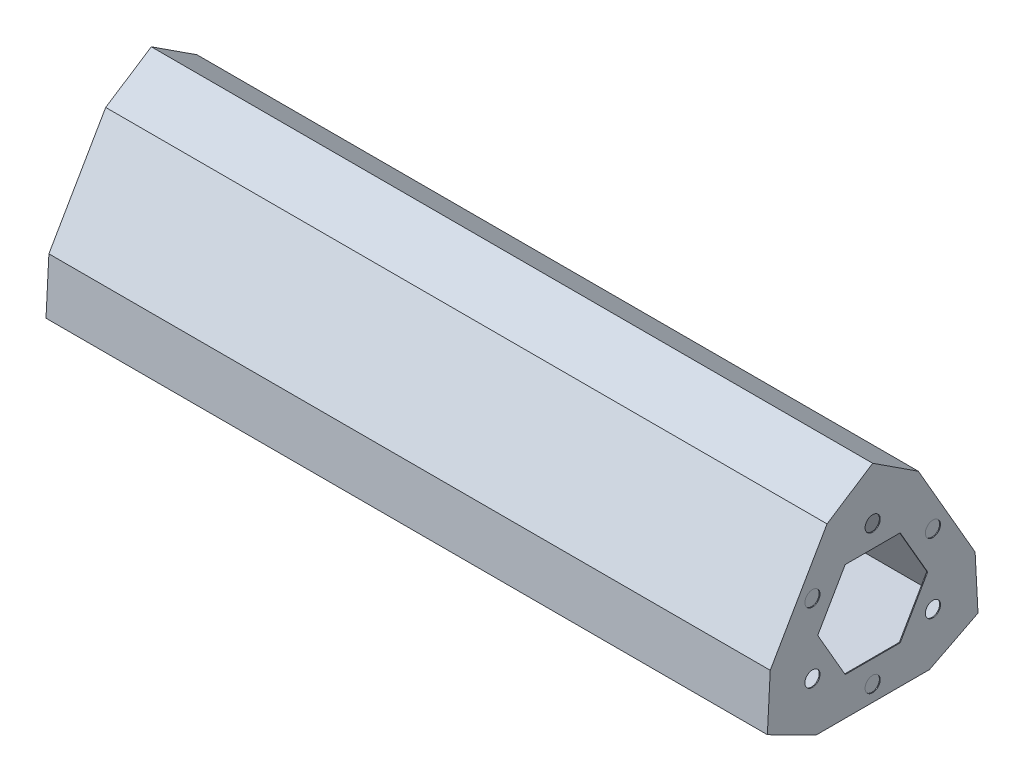
SolidWorks part; units mm, degrees
material "Polyethylene Cross-Linked"
ref_plane "Front Plane" through (0, 0, 0) normal (0, 0, 1) x (1, 0, 0)
ref_plane "Top Plane" through (0, 0, 0) normal (0, 1, 0) x (1, 0, 0)
ref_plane "Right Plane" through (0, 0, 0) normal (1, 0, 0) x (0, 0, -1)
sketch "Sketch1" plane through (0, 0, 0) normal (1, 0, 0) x (0, 0, -1)
  line L0 (0, 0) -> (44.5, 0)
  line L1 (0, 0) -> (22.25, 38.5381)
  line L2 (22.25, 38.5381) -> (44.5, 0)
  line L3 (0.6094, 11.4838) -> (12.6094, 32.2685)
  line L4 (12.6094, 32.2685) -> (22.25, 38.5381)
  line L5 (0.6094, 11.4838) -> (0, 0)
  line L6 (0, 0) -> (10.25, -5.2142)
  line L7 (10.25, -5.2142) -> (34.25, -5.2142)
  line L8 (34.25, -5.2142) -> (44.5, 0)
  line L9 (44.5, 0) -> (43.8906, 11.4838)
  line L10 (43.8906, 11.4838) -> (31.8906, 32.2685)
  line L11 (31.8906, 32.2685) -> (22.25, 38.5381)
  dimension "D2" = 44.5
  dimension "D4" = 60
  dimension "D5" = 60
  dimension "D6" = 24
  dimension "D7" = 11.5
extrude "Boss-Extrude1" add sketch "Sketch1" along normal blind 152.4 contours L10 L11 L2 L9 | L2 L1 L0 | L3 L5 L1 L4 | L7 L8 L0 L6
sketch "Sketch2" plane through (152.4, 0, 0) normal (1, 0, 0) x (0, 0, -1)
  line L0 (10.25, -5.2142) -> (34.25, -5.2142) construction
  line L1 (16.4417, 22.9063) -> (10.6335, 12.846)
  line L2 (10.6335, 12.846) -> (16.4417, 2.7858)
  line L3 (16.4417, 2.7858) -> (28.0583, 2.7858)
  line L4 (28.0583, 2.7858) -> (33.8665, 12.846)
  line L5 (33.8665, 12.846) -> (28.0583, 22.9063)
  line L6 (28.0583, 22.9063) -> (16.4417, 22.9063)
  line L7 (22.25, 38.5381) -> (22.25, -14.8896) construction
  line L9 (43.8906, 11.4838) -> (31.8906, 32.2685) construction
  circle A0 centre (22.25, 12.846) radius 10.0602 construction
  circle A1 centre (22.25, 27.5381) radius 1.6
  circle A7 centre (34.9737, 20.1921) radius 1.6
  circle A8 centre (34.9737, 5.5) radius 1.6
  circle A9 centre (22.25, -1.846) radius 1.6
  circle A10 centre (9.5263, 5.5) radius 1.6
  circle A11 centre (9.5263, 20.1921) radius 1.6
  dimension "D2" = 3.2
  dimension "D1" = 8
  dimension "D3" = 11
  dimension "D5" = 8
  dimension "D4" = 6
extrude "Cut-Extrude1" cut sketch "Sketch2" against normal blind 0.1778
sketch "Sketch4" plane through (152.2222, 0, 0) normal (1, 0, 0) x (0, 0, -1)
  line L4 (22.25, 22.9063) -> (22.25, 2.7858) construction
  line L5 (22.25, 36.0381) -> (2.1651, 1.25)
  line L6 (2.1651, 1.25) -> (42.3349, 1.25)
  line L7 (42.3349, 1.25) -> (22.25, 36.0381)
  line L8 (10.6335, 12.846) -> (33.3738, 12.846) construction
  line L9 (10.25, -5.2142) -> (34.25, -5.2142) construction
  line L13 (28.0583, 22.9063) -> (16.4417, 22.9063)
  line L14 (16.4417, 22.9063) -> (10.6335, 12.846)
  line L15 (10.6335, 12.846) -> (16.4417, 2.7858)
  line L16 (16.4417, 2.7858) -> (28.0583, 2.7858)
  line L17 (28.0583, 2.7858) -> (33.8665, 12.846)
  line L18 (33.8665, 12.846) -> (28.0583, 22.9063)
  line L19 (28.0583, 22.9063) -> (16.4417, 22.9063) construction
  line L20 (16.4417, 22.9063) -> (10.6335, 12.846) construction
  line L21 (10.6335, 12.846) -> (16.4417, 2.7858) construction
  line L22 (16.4417, 2.7858) -> (28.0583, 2.7858) construction
  line L23 (28.0583, 2.7858) -> (33.8665, 12.846) construction
  line L24 (33.8665, 12.846) -> (28.0583, 22.9063) construction
  circle A0 centre (22.25, 12.846) radius 11.596 construction
  point P13 (22.25, 12.846)
  dimension "D1" = 0
  dimension "D2" = 2.5
extrude "Cut-Extrude4" cut sketch "Sketch4" against normal offset from surface (152.0444 mm away) 0.1778 up to face at (0, 12.846, -22.25)
sketch "Sketch6" plane through (0, 0, 0) normal (-1, 0, 0) x (0, 0, 1)
  line L0 (-10.25, -5.2142) -> (-34.25, -5.2142) construction
  line L1 (-22.25, 22.661) -> (-30.75, 7.9386)
  line L2 (-30.75, 7.9386) -> (-13.75, 7.9386)
  line L3 (-13.75, 7.9386) -> (-22.25, 22.661)
  line L4 (-33.8665, 12.846) -> (-28.0583, 22.9063) construction
  line L5 (-28.0583, 2.7858) -> (-33.8665, 12.846) construction
  line L6 (-16.4417, 2.7858) -> (-28.0583, 2.7858) construction
  line L7 (-10.6335, 12.846) -> (-16.4417, 2.7858) construction
  line L8 (-16.4417, 22.9063) -> (-10.6335, 12.846) construction
  line L9 (-28.0583, 22.9063) -> (-16.4417, 22.9063) construction
  line L10 (-33.8665, 12.846) -> (-28.0583, 22.9063) construction
  line L11 (-28.0583, 2.7858) -> (-33.8665, 12.846) construction
  line L12 (-16.4417, 2.7858) -> (-28.0583, 2.7858) construction
  line L13 (-10.6335, 12.846) -> (-16.4417, 2.7858) construction
  line L14 (-16.4417, 22.9063) -> (-10.6335, 12.846) construction
  line L15 (-28.0583, 22.9063) -> (-16.4417, 22.9063) construction
  line L16 (-22.25, 22.9063) -> (-22.25, 2.7858) construction
  line L17 (-33.8665, 12.846) -> (-10.6335, 12.846) construction
  line L18 (-13.75, 7.9386) -> (-37.8906, 21.8761) construction
  line L19 (-43.8906, 11.4838) -> (-31.8906, 32.2685) construction
  circle A0 centre (-22.25, 12.846) radius 4.9075 construction
  circle A1 centre (-29.9641, 17.2998) radius 1.6
  circle A2 centre (-14.5359, 17.2998) radius 1.6
  circle A3 centre (-22.25, 3.9386) radius 1.6
  point P7 (-26.5, 15.2998)
  point P15 (-22.25, 12.846)
  dimension "D3" = 3.2
  dimension "D1" = 17
  dimension "D2" = 4
  dimension "D4" = 3
extrude "Cut-Extrude5" cut sketch "Sketch6" against normal up to surface (0.1778 mm away) up to face at (0.1778, 12.846, -22.25)
equation "\"HOLE_SIZE\"= 3.2mm"
equation "\"D3@Sketch6\"=\"HOLE_SIZE\""
equation "\"D2@Sketch2\"=\"HOLE_SIZE\""
